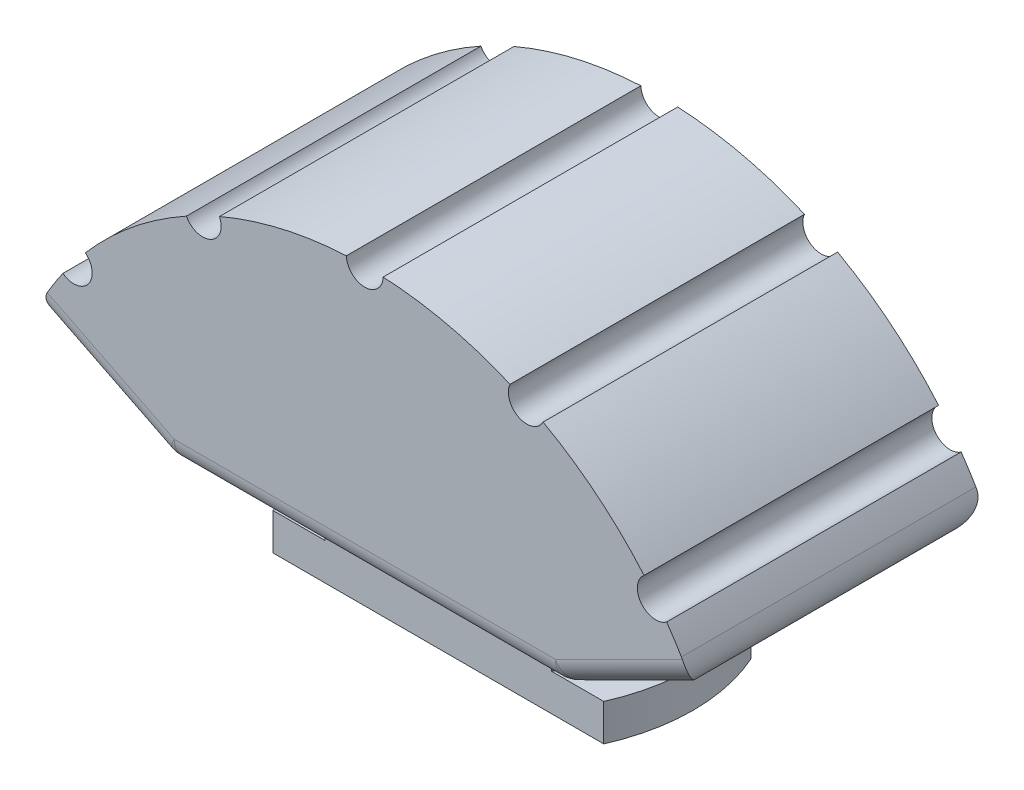
SolidWorks part; units mm, degrees
material "POLYURETHANE (11671)"
ref_plane "Front Plane" through (0, 0, 0) normal (0, 0, 1) x (1, 0, 0)
ref_plane "Top Plane" through (0, 0, 0) normal (0, 1, 0) x (1, 0, 0)
ref_plane "Right Plane" through (0, 0, 0) normal (1, 0, 0) x (0, 0, -1)
sketch "Sketch1" plane through (0, 0, 0) normal (0, 1, 0) x (1, 0, 0)
  line L1 (-14.75, -6) -> (14.75, -6)
  line L2 (-14.75, -6) -> (-14.75, 6)
  line L3 (-14.75, 6) -> (14.75, 6)
  line L4 (14.75, -6) -> (14.75, 6)
  line L5 (-14.75, -6) -> (14.75, 6) construction
  line L6 (-14.75, 6) -> (14.75, -6) construction
  point P0 (0, 0)
  dimension "D1" = 29.5
  dimension "D2" = 12
extrude "Boss-Extrude1" add sketch "Sketch1" along normal blind 3
sketch "Sketch14" plane through (0, 0, 0) normal (0, 0, 1) x (1, 0, 0)
  line L4 (0, 0) -> (-26.8328, 13.4164) construction
  line L5 (0, 0) -> (26.8328, 13.4164) construction
  line L7 (-14.75, 3) -> (14.75, 3) construction
  line L9 (0, 0) -> (0, 5.911) construction
  line L10 (-26.8328, 13.4164) -> (-16, 8)
  line L11 (-16, 8) -> (16, 8)
  line L12 (16, 8) -> (26.8328, 13.4164)
  arc A1 (26.8328, 13.4164) -> (-26.8328, 13.4164) centre (0, 0) ccw
  point P1 (6, 3)
  point P4 (-6, 3)
  dimension "D2" = 30
  dimension "D3" = 5
  dimension "D1" = 12
extrude "Boss-Extrude7" add sketch "Sketch14" along normal mid plane 24
sketch "Sketch15" plane through (0, 3, 0) normal (0, 1, 0) x (-1, 0, 0)
  line L0 (-9.2195, 6) -> (9.2195, 6)
  line L1 (9.2195, -6) -> (-9.2195, -6)
  line L2 (-14.75, -6) -> (14.75, -6) construction
  line L3 (14.75, 6) -> (-14.75, 6) construction
  circle A0 centre (0, 0) radius 11 construction
  arc A1 (-9.2195, 6) -> (-9.2195, -6) centre (0, 0) ccw
  arc A2 (9.2195, -6) -> (9.2195, 6) centre (0, 0) ccw
  dimension "D1" = 22
extrude "Boss-Extrude8" add sketch "Sketch15" along normal up to surface (5 mm away) up to face at (0, 8, 0)
sketch "Sketch16" plane through (0, 0, -12) normal (0, 0, -1) x (-1, 0, 0)
  circle A2 centre (-23.7132, 18.3762) radius 1.5
  arc A3 (26.8328, 13.4164) -> (-26.8328, 13.4164) centre (0, 0) ccw construction
  circle A4 centre (-13.2045, 26.9378) radius 1.5
  circle A5 centre (0, 30) radius 1.5
  circle A6 centre (13.2045, 26.9378) radius 1.5
  circle A7 centre (23.7132, 18.3762) radius 1.5
  point P16 (0, 0)
  point P17 (0, 0)
  point P18 (0, 0)
  point P19 (0, 0)
  point P20 (0, 0)
  dimension "D2" = 3
  dimension "D1" = 5
extrude "Cut-Extrude11" cut sketch "Sketch16" against normal up to surface (24 mm away) up to face at (0, 14.8541, 12)
fillet "Fillet5" radius 2 10 edges at (26.8328, 13.4164, 0) (-26.8328, 13.4164, 0) (16, 8, 0) (21.4164, 10.7082, 12) (21.4164, 10.7082, -12) (-21.4164, 10.7082, 12) (-16, 8, 0) (-21.4164, 10.7082, -12) (0, 8, -12) (0, 8, 12)
sketch "Sketch17" plane through (0, 0, 0) normal (0, -1, 0) x (1, 0, 0)
  line L1 (14.75, 6) -> (14.75, -6) construction
  circle A0 centre (0, 0) radius 14.75
extrude "Cut-Extrude12" cut sketch "Sketch17" against normal up to surface (3 mm away) flip side to cut up to face at (-12.4299, 3, 0)
